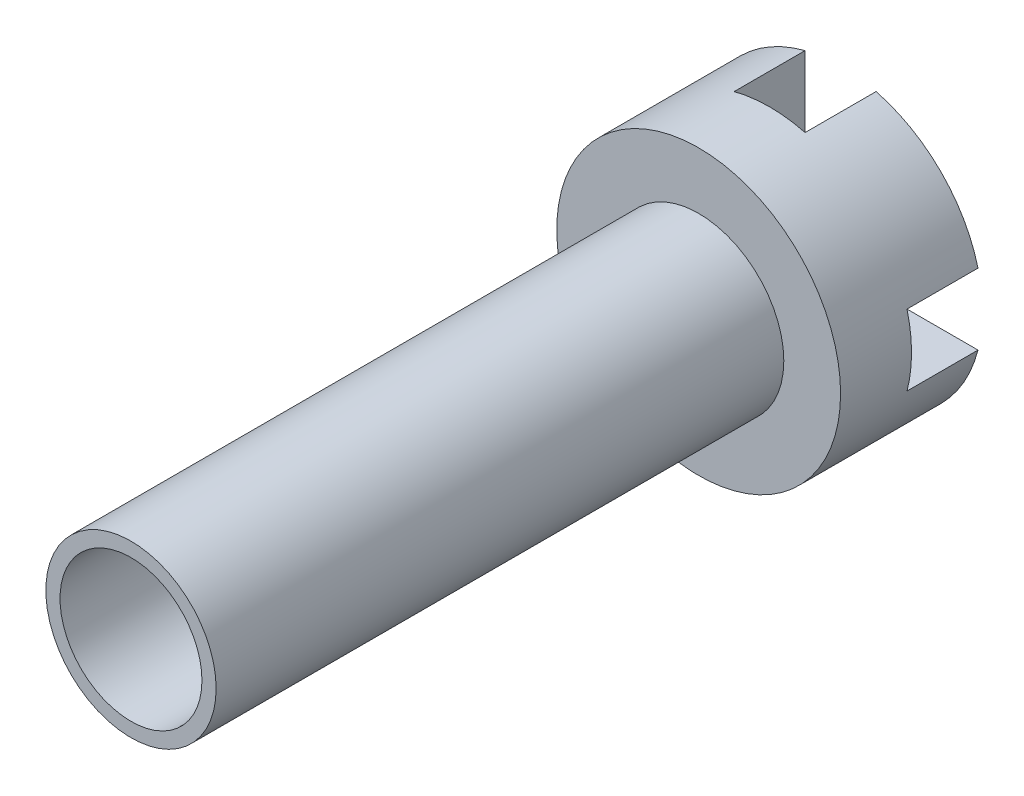
SolidWorks part; units mm, degrees
ref_plane "Plan de face" through (0, 0, 0) normal (0, 0, 1) x (1, 0, 0)
ref_plane "Plan de dessus" through (0, 0, 0) normal (0, 1, 0) x (1, 0, 0)
ref_plane "Plan de droite" through (0, 0, 0) normal (1, 0, 0) x (0, 0, -1)
sketch "Esquisse1" plane through (0, 0, 0) normal (0, 0, 1) x (1, 0, 0)
  circle A0 centre (0, 0) radius 10
  dimension "D1" = 20
extrude "Boss.-Extru.1" add sketch "Esquisse1" along normal blind 10
sketch "Esquisse2" plane through (0, 0, 10) normal (0, 0, 1) x (1, 0, 0)
  circle A0 centre (0, 0) radius 6
  dimension "D1" = 12
extrude "Boss.-Extru.2" add sketch "Esquisse2" along normal blind 40
sketch "Esquisse3" plane through (0, 0, 50) normal (0, 0, 1) x (1, 0, 0)
  circle A0 centre (0, 0) radius 5
  dimension "D1" = 10
extrude "Enlèv. mat.-Extru.1" cut sketch "Esquisse3" against normal blind 30
sketch "Esquisse5" plane through (0, 0, 0) normal (0, 0, -1) x (-1, 0, 0)
  line L1 (-10, 2.5) -> (10, 2.5)
  line L2 (-10, 2.5) -> (-10, -2.5)
  line L3 (-10, -2.5) -> (10, -2.5)
  line L4 (10, 2.5) -> (10, -2.5)
  line L5 (-2.5, 10) -> (2.5, 10)
  line L6 (-2.5, 10) -> (-2.5, -10)
  line L7 (-2.5, -10) -> (2.5, -10)
  line L8 (2.5, 10) -> (2.5, -10)
  circle M2 centre (0, 0) radius 10
  dimension "D1" = 20
  dimension "D2" = 10
  dimension "D3" = 2.5
  dimension "D4" = 5
  dimension "D5" = 5
  dimension "D6" = 20
  dimension "D7" = 10
  dimension "D8" = 2.5
extrude "Enlèv. mat.-Extru.2" cut sketch "Esquisse5" against normal blind 5 contours L8 L6 L1 M2 | L6 L1 L3 M2 | L8 L1 L6 L3 | L1 L8 L3 M2 | L8 L3 L6 M2
